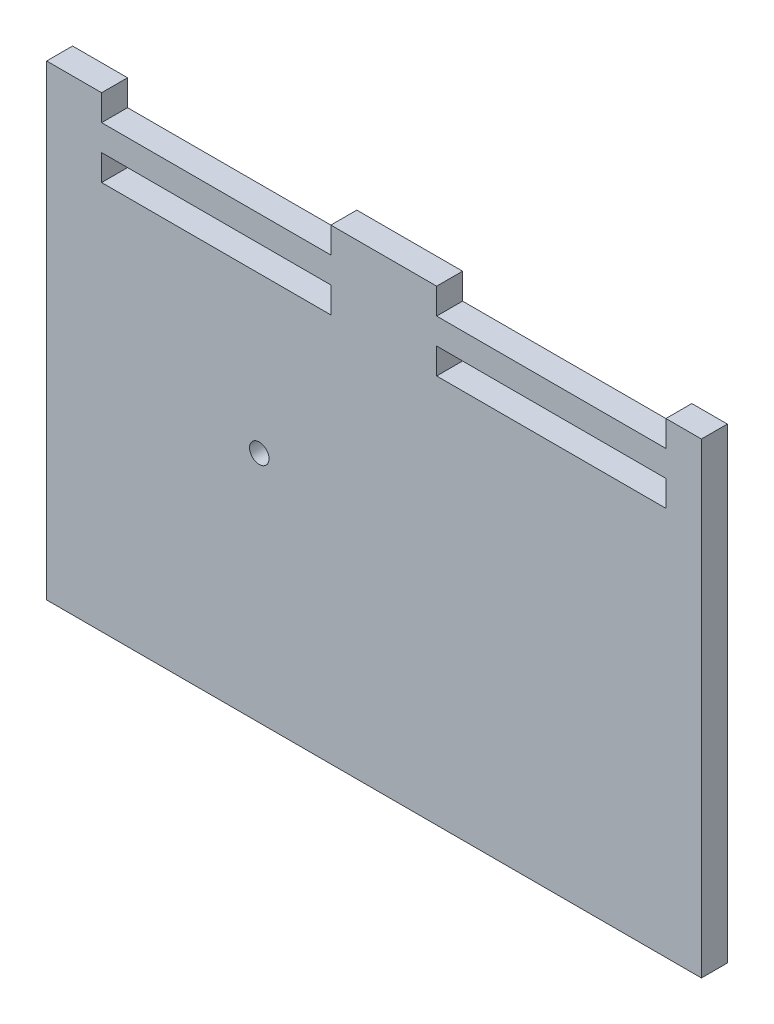
SolidWorks part; units mm, degrees
ref_plane "Front Plane" through (0, 0, 0) normal (0, 0, 1) x (1, 0, 0)
ref_plane "Top Plane" through (0, 0, 0) normal (0, 1, 0) x (1, 0, 0)
ref_plane "Right Plane" through (0, 0, 0) normal (1, 0, 0) x (0, 0, -1)
sketch "Sketch1" plane through (0, 0, 0) normal (0, 0, 1) x (1, 0, 0)
  line L1 (0, 0) -> (304.8, 0)
  line L2 (0, 0) -> (0, 228.6)
  line L3 (0, 228.6) -> (304.8, 228.6)
  line L4 (304.8, 0) -> (304.8, 228.6)
  dimension "D1" = 304.8
  dimension "D2" = 228.6
extrude "Boss-Extrude1" add sketch "Sketch1" along normal blind 12.7
sketch "Sketch2" plane through (0, 0, 12.7) normal (0, 0, 1) x (1, 0, 0)
  line L0 (304.8, 228.6) -> (0, 228.6) construction
  line L1 (0, 228.6) -> (0, 0) construction
  circle A0 centre (91.44, 114.3) radius 4.7625
  dimension "D1" = 9.525
  dimension "D2" = 114.3
  dimension "D3" = 91.44
extrude "Cut-Extrude1" cut sketch "Sketch2" against normal blind 12.7
sketch "Sketch6" plane through (0, 0, 12.7) normal (0, 0, 1) x (1, 0, 0)
  line L0 (0, 114.3) -> (304.8, 114.3) construction
  line L1 (0, 228.6) -> (0, 0) construction
  line L2 (304.8, 0) -> (304.8, 228.6) construction
sketch "Sketch7" plane through (0, 0, 12.7) normal (0, 0, 1) x (1, 0, 0)
  line L1 (14.224, 228.6) -> (126.492, 228.6)
  line L2 (14.224, 228.6) -> (14.224, 215.9)
  line L3 (14.224, 215.9) -> (126.492, 215.9)
  line L4 (0, 228.6) -> (0, 0)
  line L5 (0, 0) -> (304.8, 0)
  line L6 (304.8, 0) -> (304.8, 228.6)
  line L7 (304.8, 228.6) -> (0, 228.6)
  line L8 (0, 228.6) -> (0, 0)
  line L9 (0, 0) -> (304.8, 0)
  line L10 (304.8, 0) -> (304.8, 228.6)
  line L11 (304.8, 228.6) -> (0, 228.6)
  line L12 (126.492, 228.6) -> (126.492, 215.9)
  line L13 (178.308, 228.6) -> (290.576, 228.6)
  line L14 (178.308, 228.6) -> (178.308, 215.9)
  line L15 (178.308, 215.9) -> (290.576, 215.9)
  line L16 (290.576, 228.6) -> (290.576, 215.9)
  line L17 (14.224, 203.2) -> (126.492, 203.2)
  line L18 (14.224, 203.2) -> (14.224, 190.5)
  line L19 (14.224, 190.5) -> (126.492, 190.5)
  line L20 (126.492, 203.2) -> (126.492, 190.5)
  line L21 (178.308, 203.2) -> (290.576, 203.2)
  line L22 (178.308, 203.2) -> (178.308, 190.5)
  line L23 (178.308, 190.5) -> (290.576, 190.5)
  line L24 (290.576, 203.2) -> (290.576, 190.5)
  point P20 (70.358, 203.2)
  line M17 (304.8, 228.6) -> (0, 228.6)
  dimension "D2" = 14.224
  dimension "D3" = 112.268
  dimension "D4" = 112.268
  dimension "D5" = 14.224
  dimension "D6" = 12.7
  dimension "D7" = 12.7
  dimension "D8" = 12.7
  dimension "D9" = 112.268
  dimension "D10" = 112.268
  dimension "D11" = 12.7
  dimension "D12" = 12.7
  dimension "D1" = 0
extrude "Cut-Extrude2" cut sketch "Sketch7" against normal blind 12.7 contours L12 L2 L3 M17 | L15 L16 L13 L14 | L18 L17 L20 L19 | L22 L21 L24 L23
sketch "Sketch8" plane through (0, 0, 12.7) normal (0, 0, 1) x (1, 0, 0)
  line L1 (304.8, 228.6) -> (307.975, 228.6)
  line L2 (304.8, 228.6) -> (304.8, 0)
  line L3 (304.8, 0) -> (307.975, 0)
  line L4 (307.975, 228.6) -> (307.975, 0)
  line L5 (0, 228.6) -> (-12.7, 228.6)
  line L6 (0, 228.6) -> (0, 0)
  line L7 (0, 0) -> (-12.7, 0)
  line L8 (-12.7, 228.6) -> (-12.7, 0)
  line L12 (290.576, 215.9) -> (178.308, 215.9)
  line L13 (178.308, 215.9) -> (178.308, 228.6)
  line L14 (178.308, 228.6) -> (126.492, 228.6)
  line L15 (126.492, 228.6) -> (126.492, 215.9)
  line L16 (126.492, 215.9) -> (14.224, 215.9)
  line L17 (14.224, 215.9) -> (14.224, 228.6)
  line L18 (14.224, 228.6) -> (0, 228.6)
  line L19 (0, 228.6) -> (0, 0)
  line L20 (0, 0) -> (304.8, 0)
  line L21 (304.8, 0) -> (304.8, 228.6)
  line L22 (304.8, 228.6) -> (290.576, 228.6)
  line L23 (290.576, 228.6) -> (290.576, 215.9)
  line L24 (290.576, 215.9) -> (178.308, 215.9)
  line L25 (178.308, 215.9) -> (178.308, 228.6)
  line L26 (178.308, 228.6) -> (126.492, 228.6)
  line L27 (126.492, 228.6) -> (126.492, 215.9)
  line L28 (126.492, 215.9) -> (14.224, 215.9)
  line L29 (14.224, 215.9) -> (14.224, 228.6)
  line L30 (14.224, 228.6) -> (0, 228.6)
  line L31 (0, 228.6) -> (0, 0)
  line L32 (0, 0) -> (304.8, 0)
  line L33 (304.8, 0) -> (304.8, 228.6)
  line L34 (304.8, 228.6) -> (290.576, 228.6)
  line L35 (290.576, 228.6) -> (290.576, 215.9)
  line M22 (0, 228.6) -> (0, 0)
  line M24 (304.8, 0) -> (304.8, 228.6)
  dimension "D2" = 12.7
  dimension "D3" = 3.175
  dimension "D1" = 0
extrude "Boss-Extrude2" add sketch "Sketch8" against normal blind 12.7 contours L5 L8 L7 M22 | L4 L1 L3 M24
